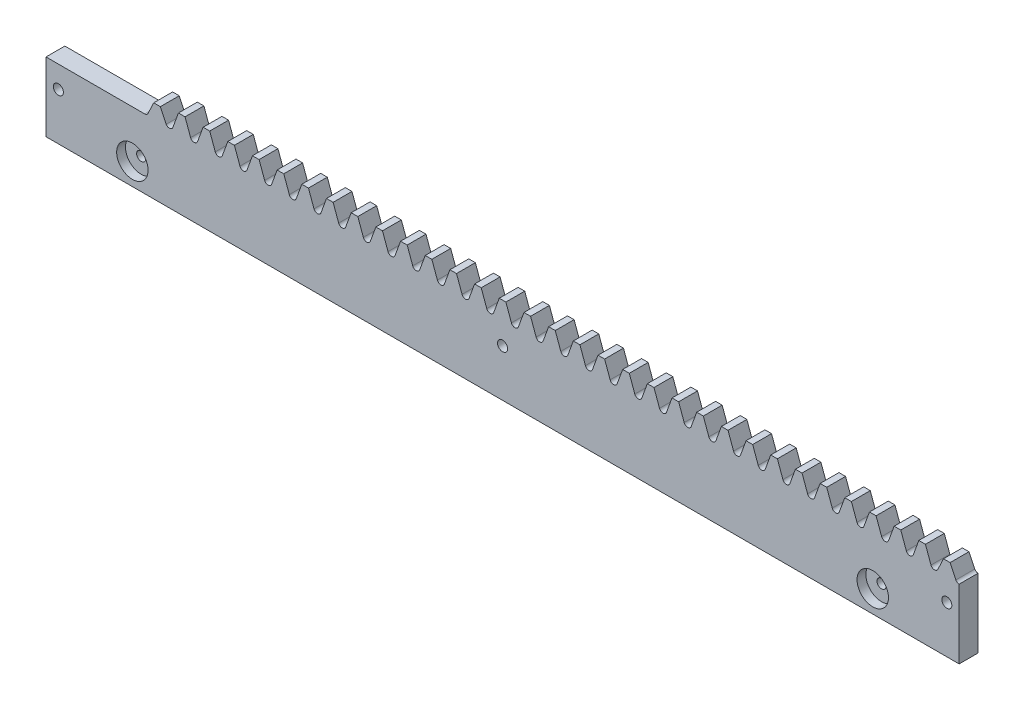
SolidWorks part; units mm, degrees
ref_plane "Plane1" through (0, 0, 0) normal (0, 0, 1) x (1, 0, 0)
ref_plane "Plane2" through (0, 0, 0) normal (0, 1, 0) x (1, 0, 0)
ref_plane "Plane3" through (0, 0, 0) normal (1, 0, 0) x (0, 0, -1)
sketch "Esquisse1" plane through (0, 0, 0) normal (0, 0, 1) x (1, 0, 0)
  line L0 (-11.781, 22) -> (19.635, 22)
  line L1 (23.5619, 29.1362) -> (23.5619, 19.2192) construction
  line L2 (-16.2297, 22) -> (24.6155, 22) construction
  line L3 (18.2522, 26.5) -> (283.3605, 26.5) construction
  line L4 (22.5084, 28.8854) -> (22.5084, 23.1798) construction
  line L5 (22.5084, 26.5) -> (20.6365, 22.5562)
  line L6 (24.6155, 26.5) -> (26.4874, 22.5562)
  line L7 (-29.4776, 0) -> (286.0574, 0) construction
  line L8 (22.5084, 26.5) -> (24.6155, 26.5)
  line L10 (275.9429, 26.742) -> (275.9429, 19.9201) construction
  line L11 (273.8358, 26.742) -> (273.8358, 19.9201) construction
  line L12 (273.8358, 26.5) -> (272.0069, 22.6314)
  line L13 (275.9429, 26.5) -> (277.7718, 22.6314)
  line L14 (273.8358, 26.5) -> (275.9429, 26.5)
  line L20 (28.5976, 22.7763) -> (30.3624, 27.625)
  line L21 (30.3624, 27.625) -> (32.4695, 27.625)
  line L22 (34.2343, 22.7763) -> (32.4695, 27.625)
  line L23 (36.4515, 22.7763) -> (38.2163, 27.625)
  line L24 (38.2163, 27.625) -> (40.3235, 27.625)
  line L25 (42.0883, 22.7763) -> (40.3235, 27.625)
  line L26 (44.3055, 22.7763) -> (46.0703, 27.625)
  line L27 (46.0703, 27.625) -> (48.1775, 27.625)
  line L28 (49.9423, 22.7763) -> (48.1775, 27.625)
  line L29 (52.1595, 22.7763) -> (53.9243, 27.625)
  line L30 (53.9243, 27.625) -> (56.0314, 27.625)
  line L31 (57.7962, 22.7763) -> (56.0314, 27.625)
  line L32 (60.0135, 22.7763) -> (61.7783, 27.625)
  line L33 (61.7783, 27.625) -> (63.8854, 27.625)
  line L34 (65.6502, 22.7763) -> (63.8854, 27.625)
  line L35 (67.8675, 22.7763) -> (69.6323, 27.625)
  line L36 (69.6323, 27.625) -> (71.7394, 27.625)
  line L37 (73.5042, 22.7763) -> (71.7394, 27.625)
  line L38 (75.7215, 22.7763) -> (77.4862, 27.625)
  line L39 (77.4862, 27.625) -> (79.5934, 27.625)
  line L40 (81.3582, 22.7763) -> (79.5934, 27.625)
  line L41 (83.5754, 22.7763) -> (85.3402, 27.625)
  line L42 (85.3402, 27.625) -> (87.4474, 27.625)
  line L43 (89.2122, 22.7763) -> (87.4474, 27.625)
  line L44 (91.4294, 22.7763) -> (93.1942, 27.625)
  line L45 (93.1942, 27.625) -> (95.3013, 27.625)
  line L46 (97.0661, 22.7763) -> (95.3013, 27.625)
  line L47 (99.2834, 22.7763) -> (101.0482, 27.625)
  line L48 (101.0482, 27.625) -> (103.1553, 27.625)
  line L49 (104.9201, 22.7763) -> (103.1553, 27.625)
  line L50 (107.1374, 22.7763) -> (108.9022, 27.625)
  line L51 (108.9022, 27.625) -> (111.0093, 27.625)
  line L52 (112.7741, 22.7763) -> (111.0093, 27.625)
  line L53 (114.9914, 22.7763) -> (116.7562, 27.625)
  line L54 (116.7562, 27.625) -> (118.8633, 27.625)
  line L55 (120.6281, 22.7763) -> (118.8633, 27.625)
  line L56 (122.8453, 22.7763) -> (124.6101, 27.625)
  line L57 (124.6101, 27.625) -> (126.7173, 27.625)
  line L58 (128.4821, 22.7763) -> (126.7173, 27.625)
  line L59 (130.6993, 22.7763) -> (132.4641, 27.625)
  line L60 (132.4641, 27.625) -> (134.5713, 27.625)
  line L61 (136.3361, 22.7763) -> (134.5713, 27.625)
  line L62 (138.5533, 22.7763) -> (140.3181, 27.625)
  line L63 (140.3181, 27.625) -> (142.4252, 27.625)
  line L64 (144.19, 22.7763) -> (142.4252, 27.625)
  line L65 (146.4073, 22.7763) -> (148.1721, 27.625)
  line L66 (148.1721, 27.625) -> (150.2792, 27.625)
  line L67 (152.044, 22.7763) -> (150.2792, 27.625)
  line L68 (154.2613, 22.7763) -> (156.0261, 27.625)
  line L69 (156.0261, 27.625) -> (158.1332, 27.625)
  line L70 (159.898, 22.7763) -> (158.1332, 27.625)
  line L71 (162.1153, 22.7763) -> (163.88, 27.625)
  line L72 (163.88, 27.625) -> (165.9872, 27.625)
  line L73 (167.752, 22.7763) -> (165.9872, 27.625)
  line L74 (169.9692, 22.7763) -> (171.734, 27.625)
  line L75 (171.734, 27.625) -> (173.8412, 27.625)
  line L76 (175.606, 22.7763) -> (173.8412, 27.625)
  line L77 (177.8232, 22.7763) -> (179.588, 27.625)
  line L78 (179.588, 27.625) -> (181.6951, 27.625)
  line L79 (183.4599, 22.7763) -> (181.6951, 27.625)
  line L80 (185.6772, 22.7763) -> (187.442, 27.625)
  line L81 (187.442, 27.625) -> (189.5491, 27.625)
  line L82 (191.3139, 22.7763) -> (189.5491, 27.625)
  line L83 (193.5312, 22.7763) -> (195.296, 27.625)
  line L84 (195.296, 27.625) -> (197.4031, 27.625)
  line L85 (199.1679, 22.7763) -> (197.4031, 27.625)
  line L86 (201.3852, 22.7763) -> (203.15, 27.625)
  line L87 (203.15, 27.625) -> (205.2571, 27.625)
  line L88 (207.0219, 22.7763) -> (205.2571, 27.625)
  line L89 (209.2391, 22.7763) -> (211.0039, 27.625)
  line L90 (211.0039, 27.625) -> (213.1111, 27.625)
  line L91 (214.8759, 22.7763) -> (213.1111, 27.625)
  line L92 (217.0931, 22.7763) -> (218.8579, 27.625)
  line L93 (218.8579, 27.625) -> (220.9651, 27.625)
  line L94 (222.7298, 22.7763) -> (220.9651, 27.625)
  line L95 (224.9471, 22.7763) -> (226.7119, 27.625)
  line L96 (226.7119, 27.625) -> (228.819, 27.625)
  line L97 (230.5838, 22.7763) -> (228.819, 27.625)
  line L98 (232.8011, 22.7763) -> (234.5659, 27.625)
  line L99 (234.5659, 27.625) -> (236.673, 27.625)
  line L100 (238.4378, 22.7763) -> (236.673, 27.625)
  line L101 (240.6551, 22.7763) -> (242.4199, 27.625)
  line L102 (242.4199, 27.625) -> (244.527, 27.625)
  line L103 (246.2918, 22.7763) -> (244.527, 27.625)
  line L104 (248.509, 22.7763) -> (250.2738, 27.625)
  line L105 (250.2738, 27.625) -> (252.381, 27.625)
  line L106 (254.1458, 22.7763) -> (252.381, 27.625)
  line L107 (256.363, 22.7763) -> (258.1278, 27.625)
  line L108 (258.1278, 27.625) -> (260.235, 27.625)
  line L109 (261.9998, 22.7763) -> (260.235, 27.625)
  line L110 (264.217, 22.7763) -> (265.9818, 27.625)
  line L111 (265.9818, 27.625) -> (268.0889, 27.625)
  line L112 (269.8537, 22.7763) -> (268.0889, 27.625)
  line L113 (-11.781, 27.0667) -> (-11.781, -40.6674) construction
  line L114 (19.635, 37.0607) -> (19.635, -15.8181) construction
  line L115 (283.3605, 22) -> (228.0591, 22) construction
  line L116 (278.8163, 26.742) -> (278.8163, -7.4189) construction
  line L118 (-11.781, 22) -> (-11.781, 0)
  line L121 (278.8163, 22) -> (278.8163, 0)
  line L122 (269.8537, 22.7763) -> (268.0889, 27.625) [skipped]
  line L123 (265.9818, 27.625) -> (268.0889, 27.625) [skipped]
  line L124 (264.217, 22.7763) -> (265.9818, 27.625) [skipped]
  line L125 (258.1278, 27.625) -> (260.235, 27.625) [skipped]
  line L126 (250.2738, 27.625) -> (252.381, 27.625) [skipped]
  line L127 (254.1458, 22.7763) -> (252.381, 27.625) [skipped]
  line L128 (256.363, 22.7763) -> (258.1278, 27.625) [skipped]
  line L129 (261.9998, 22.7763) -> (260.235, 27.625) [skipped]
  line L130 (248.509, 22.7763) -> (250.2738, 27.625) [skipped]
  line L131 (278.8163, 0) -> (-11.781, 0)
  line L132 (133.5177, 28.2837) -> (133.5177, 9.5143) construction
  line L133 (130.5371, 22) -> (141.4123, 22) construction
  line L134 (-45.8284, 15) -> (286.0574, 15) construction
  line L135 (-7.854, 23.9583) -> (-7.854, 12.1613) construction
  line L136 (274.8894, 25.9335) -> (274.8894, 12.5592) construction
  line L137 (-2.8184, 22.7763) -> (-1.0536, 27.625) [skipped]
  line L138 (-1.0536, 27.625) -> (1.0536, 27.625) [skipped]
  line L139 (2.8184, 22.7763) -> (1.0536, 27.625) [skipped]
  line L140 (5.0356, 22.7763) -> (6.8004, 27.625) [skipped]
  line L141 (6.8004, 27.625) -> (8.9076, 27.625) [skipped]
  line L142 (10.6723, 22.7763) -> (8.9076, 27.625) [skipped]
  line L143 (12.8896, 22.7763) -> (14.6544, 27.625) [skipped]
  line L144 (14.6544, 27.625) -> (16.7615, 27.625) [skipped]
  line L145 (18.5263, 22.7763) -> (16.7615, 27.625) [skipped]
  line L146 (22.5084, 27.625) -> (24.6155, 27.625) [skipped]
  line L147 (26.3803, 22.7763) -> (24.6155, 27.625) [skipped]
  line L148 (20.7436, 22.7763) -> (22.5084, 27.625) [skipped]
  line L149 (273.8358, 27.625) -> (275.9429, 27.625) [skipped]
  line L150 (277.7077, 22.7763) -> (275.9429, 27.625) [skipped]
  line L151 (272.071, 22.7763) -> (273.8358, 27.625) [skipped]
  arc A7 (19.635, 22) -> (20.6365, 22.5562) centre (19.635, 23.1798) ccw
  arc A8 (27.4889, 22) -> (26.4874, 22.5562) centre (27.4889, 23.1798) cw
  arc A9 (27.4889, 22) -> (28.5976, 22.7763) centre (27.4889, 23.1798) ccw
  arc A10 (35.3429, 22) -> (34.2343, 22.7763) centre (35.3429, 23.1798) cw
  arc A11 (35.3429, 22) -> (36.4515, 22.7763) centre (35.3429, 23.1798) ccw
  arc A12 (43.1969, 22) -> (42.0883, 22.7763) centre (43.1969, 23.1798) cw
  arc A13 (43.1969, 22) -> (44.3055, 22.7763) centre (43.1969, 23.1798) ccw
  arc A14 (51.0509, 22) -> (49.9423, 22.7763) centre (51.0509, 23.1798) cw
  arc A15 (51.0509, 22) -> (52.1595, 22.7763) centre (51.0509, 23.1798) ccw
  arc A16 (58.9049, 22) -> (57.7962, 22.7763) centre (58.9049, 23.1798) cw
  arc A17 (58.9049, 22) -> (60.0135, 22.7763) centre (58.9049, 23.1798) ccw
  arc A18 (66.7588, 22) -> (65.6502, 22.7763) centre (66.7588, 23.1798) cw
  arc A19 (66.7588, 22) -> (67.8675, 22.7763) centre (66.7588, 23.1798) ccw
  arc A20 (74.6128, 22) -> (73.5042, 22.7763) centre (74.6128, 23.1798) cw
  arc A21 (74.6128, 22) -> (75.7215, 22.7763) centre (74.6128, 23.1798) ccw
  arc A22 (82.4668, 22) -> (81.3582, 22.7763) centre (82.4668, 23.1798) cw
  arc A23 (82.4668, 22) -> (83.5754, 22.7763) centre (82.4668, 23.1798) ccw
  arc A24 (90.3208, 22) -> (89.2122, 22.7763) centre (90.3208, 23.1798) cw
  arc A25 (90.3208, 22) -> (91.4294, 22.7763) centre (90.3208, 23.1798) ccw
  arc A26 (98.1748, 22) -> (97.0661, 22.7763) centre (98.1748, 23.1798) cw
  arc A27 (98.1748, 22) -> (99.2834, 22.7763) centre (98.1748, 23.1798) ccw
  arc A28 (106.0288, 22) -> (104.9201, 22.7763) centre (106.0288, 23.1798) cw
  arc A29 (106.0288, 22) -> (107.1374, 22.7763) centre (106.0288, 23.1798) ccw
  arc A30 (113.8827, 22) -> (112.7741, 22.7763) centre (113.8827, 23.1798) cw
  arc A31 (113.8827, 22) -> (114.9914, 22.7763) centre (113.8827, 23.1798) ccw
  arc A32 (121.7367, 22) -> (120.6281, 22.7763) centre (121.7367, 23.1798) cw
  arc A33 (121.7367, 22) -> (122.8453, 22.7763) centre (121.7367, 23.1798) ccw
  arc A34 (129.5907, 22) -> (128.4821, 22.7763) centre (129.5907, 23.1798) cw
  arc A35 (129.5907, 22) -> (130.6993, 22.7763) centre (129.5907, 23.1798) ccw
  arc A36 (137.4447, 22) -> (136.3361, 22.7763) centre (137.4447, 23.1798) cw
  arc A37 (137.4447, 22) -> (138.5533, 22.7763) centre (137.4447, 23.1798) ccw
  arc A38 (145.2987, 22) -> (144.19, 22.7763) centre (145.2987, 23.1798) cw
  arc A39 (145.2987, 22) -> (146.4073, 22.7763) centre (145.2987, 23.1798) ccw
  arc A40 (153.1526, 22) -> (152.044, 22.7763) centre (153.1526, 23.1798) cw
  arc A41 (153.1526, 22) -> (154.2613, 22.7763) centre (153.1526, 23.1798) ccw
  arc A42 (161.0066, 22) -> (159.898, 22.7763) centre (161.0066, 23.1798) cw
  arc A43 (161.0066, 22) -> (162.1153, 22.7763) centre (161.0066, 23.1798) ccw
  arc A44 (168.8606, 22) -> (167.752, 22.7763) centre (168.8606, 23.1798) cw
  arc A45 (168.8606, 22) -> (169.9692, 22.7763) centre (168.8606, 23.1798) ccw
  arc A46 (176.7146, 22) -> (175.606, 22.7763) centre (176.7146, 23.1798) cw
  arc A47 (176.7146, 22) -> (177.8232, 22.7763) centre (176.7146, 23.1798) ccw
  arc A48 (184.5686, 22) -> (183.4599, 22.7763) centre (184.5686, 23.1798) cw
  arc A49 (184.5686, 22) -> (185.6772, 22.7763) centre (184.5686, 23.1798) ccw
  arc A50 (192.4226, 22) -> (191.3139, 22.7763) centre (192.4226, 23.1798) cw
  arc A51 (192.4226, 22) -> (193.5312, 22.7763) centre (192.4226, 23.1798) ccw
  arc A52 (200.2765, 22) -> (199.1679, 22.7763) centre (200.2765, 23.1798) cw
  arc A53 (200.2765, 22) -> (201.3852, 22.7763) centre (200.2765, 23.1798) ccw
  arc A54 (208.1305, 22) -> (207.0219, 22.7763) centre (208.1305, 23.1798) cw
  arc A55 (208.1305, 22) -> (209.2391, 22.7763) centre (208.1305, 23.1798) ccw
  arc A56 (215.9845, 22) -> (214.8759, 22.7763) centre (215.9845, 23.1798) cw
  arc A57 (215.9845, 22) -> (217.0931, 22.7763) centre (215.9845, 23.1798) ccw
  arc A58 (223.8385, 22) -> (222.7298, 22.7763) centre (223.8385, 23.1798) cw
  arc A59 (223.8385, 22) -> (224.9471, 22.7763) centre (223.8385, 23.1798) ccw
  arc A60 (231.6925, 22) -> (230.5838, 22.7763) centre (231.6925, 23.1798) cw
  arc A61 (231.6925, 22) -> (232.8011, 22.7763) centre (231.6925, 23.1798) ccw
  arc A62 (239.5464, 22) -> (238.4378, 22.7763) centre (239.5464, 23.1798) cw
  arc A63 (239.5464, 22) -> (240.6551, 22.7763) centre (239.5464, 23.1798) ccw
  arc A64 (247.4004, 22) -> (246.2918, 22.7763) centre (247.4004, 23.1798) cw
  arc A65 (247.4004, 22) -> (248.509, 22.7763) centre (247.4004, 23.1798) ccw
  arc A66 (255.2544, 22) -> (254.1458, 22.7763) centre (255.2544, 23.1798) cw
  arc A67 (255.2544, 22) -> (256.363, 22.7763) centre (255.2544, 23.1798) ccw
  arc A68 (263.1084, 22) -> (261.9998, 22.7763) centre (263.1084, 23.1798) cw
  arc A69 (263.1084, 22) -> (264.217, 22.7763) centre (263.1084, 23.1798) ccw
  arc A70 (270.9624, 22) -> (269.8537, 22.7763) centre (270.9624, 23.1798) cw
  arc A72 (270.9624, 22) -> (272.0069, 22.6314) centre (270.9624, 23.1798) ccw
  arc A73 (270.9624, 22) -> (269.8537, 22.7763) centre (270.9624, 23.1798) cw [skipped]
  arc A74 (255.2544, 22) -> (254.1458, 22.7763) centre (255.2544, 23.1798) cw [skipped]
  arc A75 (255.2544, 22) -> (256.363, 22.7763) centre (255.2544, 23.1798) ccw [skipped]
  arc A76 (263.1084, 22) -> (261.9998, 22.7763) centre (263.1084, 23.1798) cw [skipped]
  arc A77 (263.1084, 22) -> (264.217, 22.7763) centre (263.1084, 23.1798) ccw [skipped]
  arc A78 (247.4004, 22) -> (248.509, 22.7763) centre (247.4004, 23.1798) ccw [skipped]
  arc A79 (278.8163, 22) -> (277.7718, 22.6314) centre (278.8163, 23.1798) cw
  circle A80 centre (133.5177, 15) radius 1.6
  circle A81 centre (-7.854, 15) radius 1.6
  circle A82 centre (274.8894, 15) radius 1.6
  arc A83 (19.635, 22) -> (18.5263, 22.7763) centre (19.635, 23.1798) cw [skipped]
  arc A84 (-3.927, 22) -> (-2.8184, 22.7763) centre (-3.927, 23.1798) ccw [skipped]
  arc A85 (3.927, 22) -> (2.8184, 22.7763) centre (3.927, 23.1798) cw [skipped]
  arc A86 (3.927, 22) -> (5.0356, 22.7763) centre (3.927, 23.1798) ccw [skipped]
  arc A87 (11.781, 22) -> (10.6723, 22.7763) centre (11.781, 23.1798) cw [skipped]
  arc A88 (11.781, 22) -> (12.8896, 22.7763) centre (11.781, 23.1798) ccw [skipped]
  dimension "D2" = 4.5
  dimension "D1" = 7
extrude "Extrusion1" add sketch "Esquisse1" along normal blind 6
sketch "Esquisse4" plane through (0, 0, 6) normal (0, 0, 1) x (1, 0, 0)
  line L0 (15.708, 31.1875) -> (15.708, -14.7899) construction
  line L1 (6.9611, 7) -> (270.7775, 7) construction
  line L2 (251.3274, 30.2531) -> (251.3274, -5.0048) construction
  circle A0 centre (15.708, 7) radius 5
  circle A2 centre (251.3274, 7) radius 5
extrude "Enlèv. mat.-Extru.2" cut sketch "Esquisse4" against normal blind 2.8
sketch "Esquisse5" plane through (0, 0, 3.2) normal (0, 0, 1) x (1, 0, 0)
  line L0 (15.708, 33.4411) -> (15.708, -6.3197) construction
  line L1 (9.4058, 7) -> (272.7995, 7) construction
  line L2 (251.3274, 30.3305) -> (251.3274, -6.3197) construction
  circle A0 centre (15.708, 7) radius 1.45
  circle A1 centre (251.3274, 7) radius 1.45
extrude "Enlèv. mat.-Extru.3" cut sketch "Esquisse5" against normal blind 2.5
